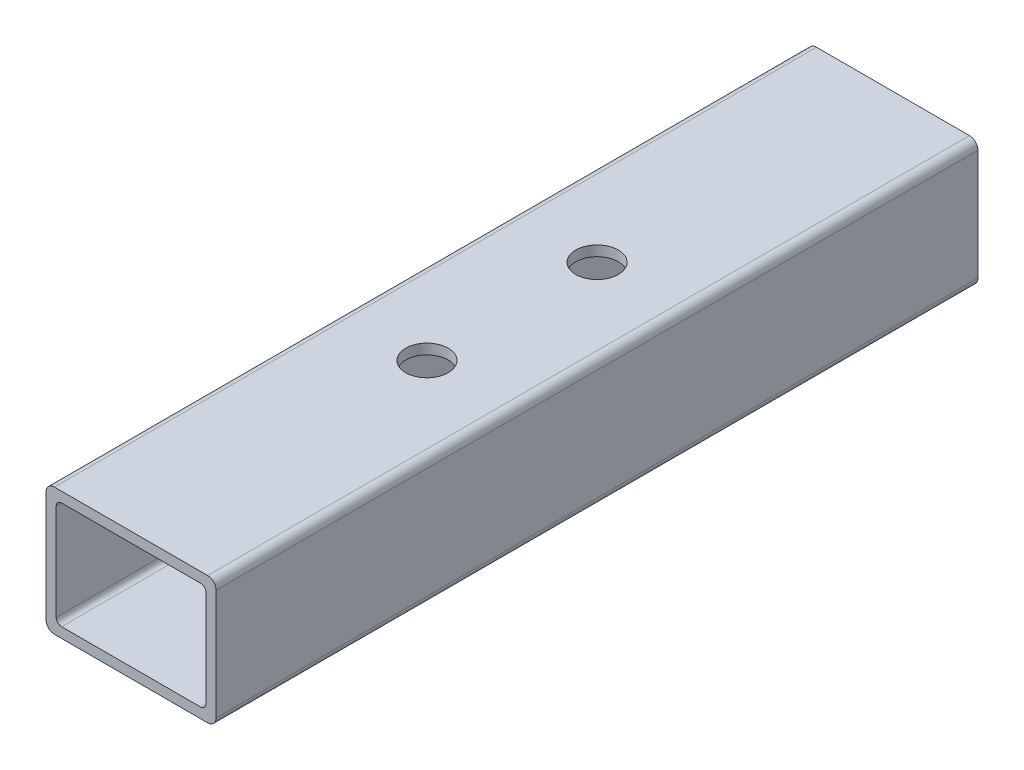
SolidWorks part; units mm, degrees
material "Plain Carbon Steel"
ref_plane "Front" through (0, 0, 0) normal (0, 0, 1) x (1, 0, 0)
ref_plane "Top" through (0, 0, 0) normal (0, 1, 0) x (1, 0, 0)
ref_plane "Right" through (0, 0, 0) normal (1, 0, 0) x (0, 0, -1)
sketch "Sketch1" plane through (0, 0, 0) normal (0, 0, 1) x (1, 0, 0)
  line L0 (-22.352, 0) -> (-25.4, 0) construction
  line L1 (22.86, -19.05) -> (-22.86, -19.05)
  line L2 (25.4, -16.51) -> (25.4, 16.51)
  line L3 (22.86, 19.05) -> (-22.86, 19.05)
  line L4 (-25.4, -16.51) -> (-25.4, 16.51)
  line L5 (25.4, -19.05) -> (-25.4, 19.05) construction
  line L6 (25.4, 19.05) -> (-25.4, -19.05) construction
  line L7 (20.7518, 16.002) -> (-20.7518, 16.002)
  line L8 (22.352, 14.4018) -> (22.352, -14.4018)
  line L9 (20.7518, -16.002) -> (-20.7518, -16.002)
  line L10 (-22.352, 14.4018) -> (-22.352, -14.4018)
  line L11 (22.352, 16.002) -> (-22.352, -16.002) construction
  line L12 (22.352, -16.002) -> (-22.352, 16.002) construction
  line L13 (0, -16.002) -> (0, -19.05) construction
  line L14 (22.352, -14.4018) -> (22.352, -19.05) construction
  line L16 (22.352, -19.05) -> (25.4, -19.05) construction
  arc A0 (-20.7518, -16.002) -> (-22.352, -14.4018) centre (-20.7518, -14.4018) cw
  arc A1 (22.352, -14.4018) -> (20.7518, -16.002) centre (20.7518, -14.4018) cw
  arc A2 (20.7518, 16.002) -> (22.352, 14.4018) centre (20.7518, 14.4018) cw
  arc A3 (-20.7518, 16.002) -> (-22.352, 14.4018) centre (-20.7518, 14.4018) ccw
  arc A4 (22.86, -19.05) -> (25.4, -16.51) centre (22.86, -16.51) ccw
  arc A5 (25.4, 16.51) -> (22.86, 19.05) centre (22.86, 16.51) ccw
  arc A6 (-22.86, 19.05) -> (-25.4, 16.51) centre (-22.86, 16.51) ccw
  arc A7 (-22.86, -19.05) -> (-25.4, -16.51) centre (-22.86, -16.51) cw
  point P0 (0, 0)
  point P6 (0, 0)
  dimension "D2" = 1.6002
  dimension "D3" = 2.54
sketch "Sketch2" plane through (0, 0, 0) normal (1, 0, 0) x (0, 0, -1)
  line L0 (-152.4, 0) -> (152.4, 0) construction
  dimension "Length" = 304.8
ref_plane "Plane1" through (25.4, 0, 0) normal (1, 0, 0) x (0, 0, -1)
sketch "Sketch5" plane through (25.4, 0, 0) normal (1, 0, 0) x (0, 0, -1)
  line L0 (-152.4, 19.05) -> (-152.4, -19.05) construction
  line L1 (152.4, 19.05) -> (152.4, -19.05) construction
sketch "Sketch4" plane through (0, 0, 0) normal (0, 0, 1) x (1, 0, 0)
  line L0 (25.4, -16.51) -> (25.4, 16.51) construction
  line L1 (22.86, 19.05) -> (-22.86, 19.05) construction
  line L2 (-25.4, -16.51) -> (-25.4, 16.51) construction
  line L3 (22.86, -19.05) -> (-22.86, -19.05) construction
  line L4 (22.352, 14.4018) -> (22.352, -14.4018) construction
  line L5 (20.7518, -16.002) -> (-20.7518, -16.002) construction
  line L6 (-22.352, 14.4018) -> (-22.352, -14.4018) construction
  line L7 (20.7518, 16.002) -> (-20.7518, 16.002) construction
  line L8 (25.4, -16.51) -> (25.4, 16.51)
  line L9 (22.86, 19.05) -> (-22.86, 19.05)
  line L10 (-25.4, -16.51) -> (-25.4, 16.51)
  line L11 (22.86, -19.05) -> (-22.86, -19.05)
  line L12 (22.352, 14.4018) -> (22.352, -14.4018)
  line L13 (20.7518, -16.002) -> (-20.7518, -16.002)
  line L14 (-22.352, 14.4018) -> (-22.352, -14.4018)
  line L15 (20.7518, 16.002) -> (-20.7518, 16.002)
  arc A0 (25.4, 16.51) -> (22.86, 19.05) centre (22.86, 16.51) ccw construction
  arc A1 (-22.86, 19.05) -> (-25.4, 16.51) centre (-22.86, 16.51) ccw construction
  arc A2 (-25.4, -16.51) -> (-22.86, -19.05) centre (-22.86, -16.51) ccw construction
  arc A3 (22.86, -19.05) -> (25.4, -16.51) centre (22.86, -16.51) ccw construction
  arc A4 (20.7518, -16.002) -> (22.352, -14.4018) centre (20.7518, -14.4018) ccw construction
  arc A5 (-22.352, -14.4018) -> (-20.7518, -16.002) centre (-20.7518, -14.4018) ccw construction
  arc A6 (-20.7518, 16.002) -> (-22.352, 14.4018) centre (-20.7518, 14.4018) ccw construction
  arc A7 (22.352, 14.4018) -> (20.7518, 16.002) centre (20.7518, 14.4018) ccw construction
  arc A8 (25.4, 16.51) -> (22.86, 19.05) centre (22.86, 16.51) ccw
  arc A9 (-22.86, 19.05) -> (-25.4, 16.51) centre (-22.86, 16.51) ccw
  arc A10 (-25.4, -16.51) -> (-22.86, -19.05) centre (-22.86, -16.51) ccw
  arc A11 (22.86, -19.05) -> (25.4, -16.51) centre (22.86, -16.51) ccw
  arc A12 (20.7518, -16.002) -> (22.352, -14.4018) centre (20.7518, -14.4018) ccw
  arc A13 (-22.352, -14.4018) -> (-20.7518, -16.002) centre (-20.7518, -14.4018) ccw
  arc A14 (-20.7518, 16.002) -> (-22.352, 14.4018) centre (-20.7518, 14.4018) ccw
  arc A15 (22.352, 14.4018) -> (20.7518, 16.002) centre (20.7518, 14.4018) ccw
extrude "Boss-Extrude1" add sketch "Sketch4" along normal blind 227.5637
sketch "Sketch6" plane through (0, 19.05, 0) normal (0, 1, 0) x (1, 0, 0)
  line L0 (0, -227.5637) -> (0, -183.6318) construction
  line L2 (-22.86, -183.6318) -> (22.86, -183.6318) construction
  line L3 (-22.86, 0) -> (-22.86, -227.5637) construction
  line L4 (22.86, 0) -> (22.86, -227.5637) construction
  line L5 (-22.86, -43.9318) -> (22.86, -43.9318) construction
  line L6 (22.86, -227.5637) -> (-22.86, -227.5637) construction
  line L7 (0, -183.6318) -> (0, -43.9318) construction
  line L8 (0, -43.9318) -> (0, 0) construction
  line L9 (22.86, 0) -> (-22.86, 0) construction
  dimension "D1" = 139.7
sketch "Sketch9" plane through (0, 19.05, 0) normal (0, 1, 0) x (1, 0, 0)
  line L0 (0, -227.5637) -> (0, -139.1818) construction
  line L1 (22.86, -227.5637) -> (-22.86, -227.5637) construction
  line L2 (0, -139.1818) -> (0, -88.3818) construction
  line L3 (0, -88.3818) -> (0, 0) construction
  circle A0 centre (0, -139.1818) radius 6.35
  circle A1 centre (0, -88.3818) radius 6.35
  dimension "D2" = 12.7
  dimension "D1" = 50.8
extrude "Cut-Extrude2" cut sketch "Sketch9" along direction (0, -1, 0) on the side against the normal up to next (3.048 mm away)
equation "\"D3@Sketch1\"=\"Outside Width@Sketch1\"*.05"
equation "\"D2@Sketch1\"=\"D1@Sketch1\"*.05"
